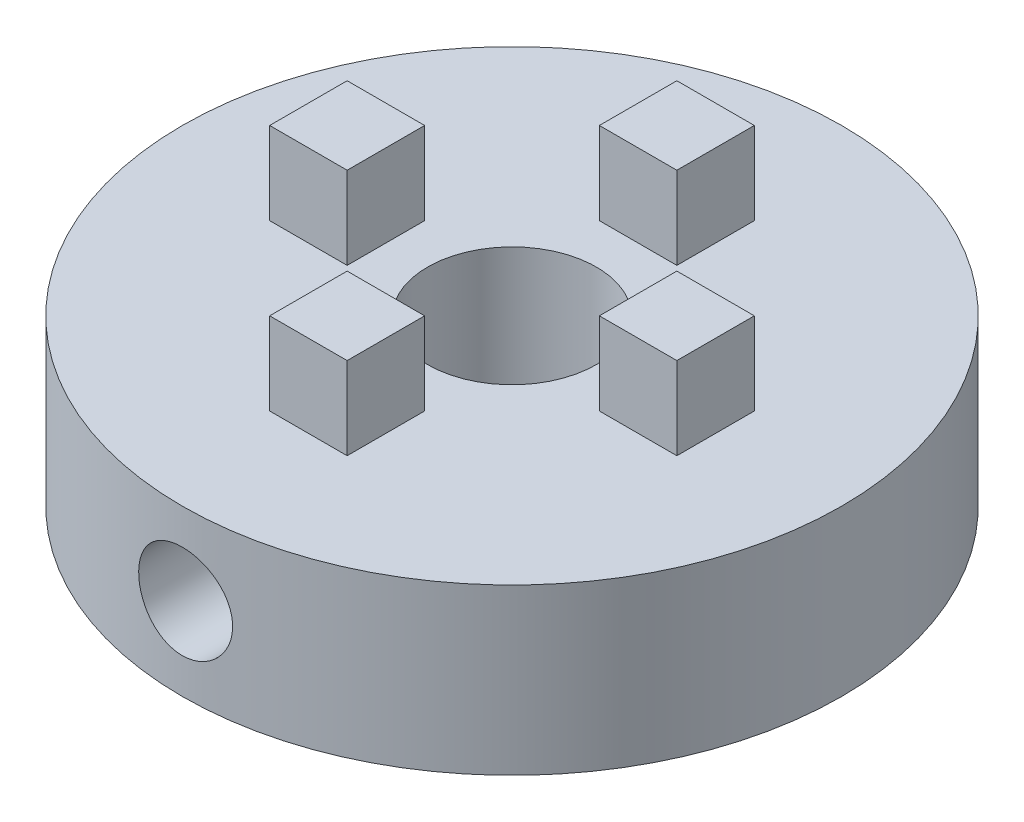
SolidWorks part; units mm, degrees
ref_plane "Front Plane" through (0, 0, 0) normal (0, 0, 1) x (1, 0, 0)
ref_plane "Top Plane" through (0, 0, 0) normal (0, 1, 0) x (1, 0, 0)
ref_plane "Right Plane" through (0, 0, 0) normal (1, 0, 0) x (0, 0, -1)
sketch "Sketch1" plane through (0, 0, 0) normal (0, 1, 0) x (1, 0, 0)
  circle A0 centre (0, 0) radius 20
  circle A1 centre (0, 0) radius 5.125
  dimension "D1" = 40
  dimension "D2" = 10.25
extrude "Boss-Extrude1" add sketch "Sketch1" along normal blind 10
sketch "Sketch2" plane through (0, 10, 0) normal (0, 1, 0) x (1, 0, 0)
  line L0 (7.65, 2.35) -> (12.35, 2.35)
  line L1 (-2.35, 7.65) -> (2.35, 7.65)
  line L2 (-2.35, 7.65) -> (-2.35, 12.35)
  line L3 (-2.35, 12.35) -> (2.35, 12.35)
  line L4 (2.35, 7.65) -> (2.35, 12.35)
  line L5 (-2.35, 7.65) -> (2.35, 12.35) construction
  line L6 (-2.35, 12.35) -> (2.35, 7.65) construction
  line L7 (7.65, 2.35) -> (7.65, -2.35)
  line L8 (7.65, -2.35) -> (12.35, -2.35)
  line L9 (12.35, 2.35) -> (12.35, -2.35)
  line L10 (2.35, -7.65) -> (2.35, -12.35)
  line L11 (2.35, -7.65) -> (-2.35, -7.65)
  line L12 (-2.35, -7.65) -> (-2.35, -12.35)
  line L13 (2.35, -12.35) -> (-2.35, -12.35)
  line L14 (-7.65, -2.35) -> (-12.35, -2.35)
  line L15 (-7.65, -2.35) -> (-7.65, 2.35)
  line L16 (-7.65, 2.35) -> (-12.35, 2.35)
  line L17 (-12.35, -2.35) -> (-12.35, 2.35)
  point P0 (0, 10)
  point P21 (0, 0)
  dimension "D1" = 4.7
  dimension "D2" = 4.7
  dimension "D3" = 10
  dimension "D4" = 4
extrude "Boss-Extrude2" add sketch "Sketch2" along normal blind 5 contours L4 L3 L2 L1
sketch "Sketch3" plane through (0, 0, 0) normal (0, 0, 1) x (1, 0, 0)
  line L0 (-20, 5) -> (20, 5) construction
  line L1 (-20, 10) -> (-20, 0) construction
  line L2 (20, 0) -> (20, 10) construction
  circle A0 centre (0, 5) radius 2
  dimension "D1" = 4
extrude "Cut-Extrude2" cut sketch "Sketch3" along normal through all
sketch "Sketch4" plane through (0, 0, 0) normal (0, 0, 1) x (1, 0, 0)
  circle A0 centre (0, 5) radius 2.85
  dimension "D1" = 5.7
extrude "Cut-Extrude3" cut sketch "Sketch4" along normal through all from offset 10
